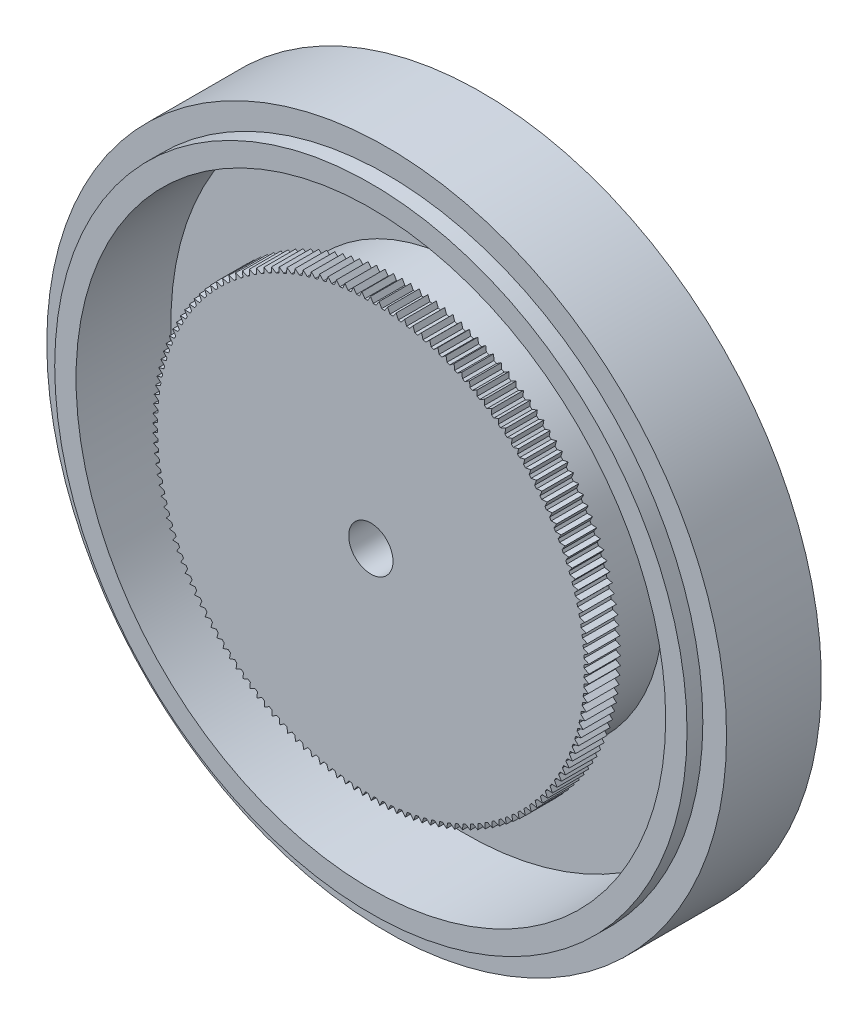
SolidWorks part; units mm, degrees
ref_plane "Front Plane" through (0, 0, 0) normal (0, 0, 1) x (1, 0, 0)
ref_plane "Top Plane" through (0, 0, 0) normal (0, 1, 0) x (1, 0, 0)
ref_plane "Right Plane" through (0, 0, 0) normal (1, 0, 0) x (0, 0, -1)
sketch "Sketch1" plane through (0, 0, 0) normal (0, 0, 1) x (1, 0, 0)
  circle A0 centre (0, 0) radius 21.5
  dimension "D1" = 43
extrude "Extrude1" add sketch "Sketch1" along normal blind 8
sketch "Sketch2" plane through (0, 0, 8) normal (0, 0, 1) x (1, 0, 0)
  circle A0 centre (0, 0) radius 18.65
  dimension "D1" = 37.3
extrude "Extrude2" cut sketch "Sketch2" against normal blind 6
sketch "Sketch3" plane through (0, 0, 2) normal (0, 0, 1) x (1, 0, 0)
  circle A0 centre (0, 0) radius 12.5
  dimension "D1" = 25
extrude "Extrude3" add sketch "Sketch3" along normal blind 4
sketch "Sketch4" plane through (0, 0, 6) normal (0, 0, 1) x (1, 0, 0)
  circle A0 centre (0, 0) radius 13.5
  dimension "D1" = 27
extrude "Extrude4" add sketch "Sketch4" along normal blind 2
sketch "Sketch7" plane through (0, 0, 8) normal (0, 0, 1) x (1, 0, 0)
  line L0 (-0.0208, 13.8) -> (-0.2518, 13.4)
  line L1 (-0.2518, 13.4) -> (0.2101, 13.4)
  line L2 (0.2101, 13.4) -> (-0.0208, 13.8)
  dimension "D1" = 0.4
  dimension "D2" = 13.4
extrude "Extrude10" add sketch "Sketch7" against normal blind 2
pattern_circular "CirPattern5" count 160 over 360 about axis through (0, 0, 0) along (0, 0, 1) of "Extrude10"
sketch "Sketch8" plane through (0, 0, 8) normal (0, 0, 1) x (1, 0, 0)
  circle A0 centre (0, 0) radius 1.4
extrude "Extrude11" cut sketch "Sketch8" against normal through all
sketch "Sketch9" plane through (0, 0, 0) normal (0, 0, -1) x (-1, 0, 0)
  circle A0 centre (0, 0) radius 20
  circle A1 centre (0, 0) radius 21.5
extrude "Extrude13" cut sketch "Sketch9" against normal blind 1
sketch "Sketch10" plane through (0, 0, 8) normal (0, 0, 1) x (1, 0, 0)
  circle A0 centre (0, 0) radius 21.5
  circle A1 centre (0, 0) radius 20
extrude "Extrude14" cut sketch "Sketch10" against normal blind 1
